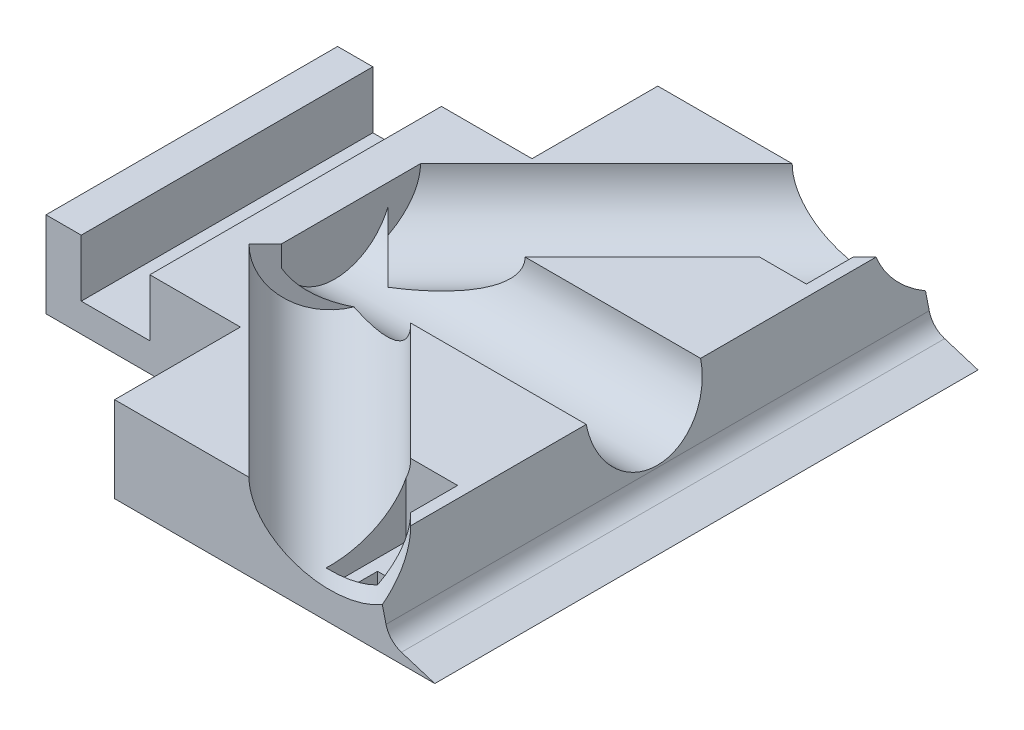
SolidWorks part; units mm, degrees
ref_plane "Front Plane" through (0, 0, 0) normal (0, 0, 1) x (1, 0, 0)
ref_plane "Top Plane" through (0, 0, 0) normal (0, 1, 0) x (1, 0, 0)
ref_plane "Right Plane" through (0, 0, 0) normal (1, 0, 0) x (0, 0, -1)
sketch "Sketch1" plane through (0, 0, 0) normal (0, 1, 0) x (1, 0, 0)
  line L1 (-45, -47.5) -> (45, -47.5)
  line L2 (-45, -47.5) -> (-45, 47.5)
  line L3 (-45, 47.5) -> (45, 47.5)
  line L4 (45, -47.5) -> (45, 47.5)
  line L5 (-45, -47.5) -> (45, 47.5) construction
  line L6 (-45, 47.5) -> (45, -47.5) construction
  point P0 (0, 0)
  dimension "D1" = 95
  dimension "D2" = 90
extrude "Boss-Extrude1" add sketch "Sketch1" along normal blind 20
sketch "Sketch2" plane through (45, 0, 0) normal (1, 0, 0) x (0, 0, -1)
  line L0 (-47.5, 0) -> (47.5, 0) construction
  line L1 (47.5, 20) -> (47.5, 0) construction
  circle A0 centre (0, 13) radius 10
  dimension "D1" = 13
  dimension "D2" = 47.5
extrude "Cut-Extrude2" cut sketch "Sketch2" against normal blind 70
sketch "Sketch3" plane through (0, 0, 47.5) normal (0, 0, 1) x (1, 0, 0)
  line L0 (45, 0) -> (37.4211, 1.8993)
  line L1 (37.4211, 1.8993) -> (30.2523, 20)
  line L2 (-45, 20) -> (45, 20) construction
  line L4 (30.2523, 20) -> (45, 20)
  line L7 (45, 20) -> (45, 0)
extrude "Cut-Extrude3" cut sketch "Sketch3" against normal blind 100
sketch "Sketch5" plane through (0, 0, 47.5) normal (0, 0, 1) x (1, 0, 0)
  line L0 (-45, 0) -> (45, 0) construction
  line L1 (-26.8384, 19) -> (-38.8384, 19)
  line L2 (-26.8384, 19) -> (-26.8384, 3)
  line L3 (-26.8384, 3) -> (-38.8384, 3)
  line L4 (-38.8384, 19) -> (-38.8384, 3)
  dimension "D1" = 12
  dimension "D2" = 3
  dimension "D3" = 16
extrude "Cut-Extrude5" cut sketch "Sketch5" against normal blind 100
fillet "Fillet2" radius 10 1 edges at (37.4211, 1.8993, 0)
sketch "Sketch6" plane through (0, 20, 0) normal (0, 1, 0) x (1, 0, 0)
  line L0 (30.2523, 47.5) -> (-45, 47.5) construction
  line L1 (-45, -47.5) -> (-21, -47.5)
  line L2 (-45, -47.5) -> (-45, 47.5)
  line L3 (-45, 47.5) -> (-21, 47.5)
  line L4 (-21, -47.5) -> (-21, 47.5)
  dimension "D1" = 24
extrude "Boss-Extrude2" add sketch "Sketch6" along normal blind 24
sketch "Sketch7" plane through (0, 20, 0) normal (0, 1, 0) x (1, 0, 0)
  line L0 (-21, -47.5) -> (30.2523, -47.5) construction
  line L1 (-19, -45.5) -> (28.2523, -45.5)
  line L2 (-19, -45.5) -> (-19, -11.5014)
  line L3 (-19, -11.5014) -> (28.2523, -11.5014)
  line L4 (28.2523, -45.5) -> (28.2523, -11.5014)
  line L5 (30.2523, -7.1414) -> (-21, -7.1414) construction
  line L6 (-21, -47.5) -> (-21, -7.1414) construction
  line L7 (30.2523, -7.1414) -> (30.2523, -47.5) construction
  dimension "D1" = 2
  dimension "D2" = 4.36
  dimension "D3" = 2
  dimension "D4" = 2
  dimension "D5" = 33.9986
extrude "Cut-Extrude7" cut sketch "Sketch7" against normal blind 17
sketch "Sketch8" plane through (0, 20, 0) normal (0, 1, 0) x (1, 0, 0)
  line L0 (30.2523, 47.5) -> (-21, 47.5) construction
  line L1 (-19, 11.5) -> (28.2523, 11.5)
  line L2 (-19, 11.5) -> (-19, 45.5)
  line L3 (-19, 45.5) -> (28.2523, 45.5)
  line L4 (28.2523, 11.5) -> (28.2523, 45.5)
  line L5 (30.2523, 47.5) -> (30.2523, 7.1414) construction
  line L6 (-21, 7.1414) -> (-21, 47.5) construction
  dimension "D1" = 2
  dimension "D2" = 34
  dimension "D3" = 2
  dimension "D4" = 2
extrude "Cut-Extrude8" cut sketch "Sketch8" against normal blind 17
sketch "Sketch10" plane through (-21, 0, 0) normal (1, 0, 0) x (0, 0, -1)
  line L1 (-47.5, 44) -> (47.5, 44)
  line L2 (-47.5, 44) -> (-47.5, 20)
  line L3 (-47.5, 20) -> (47.5, 20)
  line L4 (47.5, 44) -> (47.5, 20)
extrude "Boss-Extrude3" add sketch "Sketch10" along normal blind 25
sketch "Sketch12" plane through (-45, 0, 0) normal (-1, 0, 0) x (0, 0, 1)
  line L1 (47.5, 0) -> (25.5, 0)
  line L2 (47.5, 0) -> (47.5, 32)
  line L3 (47.5, 32) -> (25.5, 32)
  line L4 (25.5, 0) -> (25.5, 32)
  dimension "D1" = 32
  dimension "D2" = 22
extrude "Cut-Extrude9" cut sketch "Sketch12" against normal blind 34
sketch "Sketch13" plane through (-45, 0, 0) normal (-1, 0, 0) x (0, 0, 1)
  line L1 (-47.5, 0) -> (-25.5, 0)
  line L2 (-47.5, 0) -> (-47.5, 32)
  line L3 (-47.5, 32) -> (-25.5, 32)
  line L4 (-25.5, 0) -> (-25.5, 32)
  dimension "D1" = 22
  dimension "D2" = 32
extrude "Cut-Extrude10" cut sketch "Sketch13" against normal blind 34
sketch "Sketch14" plane through (0, 0, -47.5) normal (0, 0, -1) x (-1, 0, 0)
  line L0 (11, 32) -> (45, 32) construction
  circle A0 centre (31.5228, 44) radius 10
  dimension "D1" = 12
extrude "Cut-Extrude11" cut sketch "Sketch14" against normal blind 100
sketch "Sketch18" plane through (0, 0, -47.5) normal (0, 0, -1) x (-1, 0, 0)
  line L0 (11, 32) -> (45, 32) construction
  line L1 (-4, 44) -> (15.5228, 44)
  line L2 (-4, 44) -> (-4, 32)
  line L3 (-4, 32) -> (15.5228, 32)
  line L4 (15.5228, 44) -> (15.5228, 32)
  dimension "D1" = 6
extrude "Cut-Extrude13" cut sketch "Sketch18" against normal blind 100
sketch "Sketch19" plane through (-25, 0, 0) normal (1, 0, 0) x (0, 0, -1)
  circle A0 centre (0, 13) radius 10
  arc A1 (-7.1414, 20) -> (7.1414, 20) centre (0, 13) ccw construction
  dimension "D1" = 0
extrude "Boss-Extrude5" add sketch "Sketch19" along normal blind 60
sketch "Sketch20" plane through (0, 0, 47.5) normal (0, 0, 1) x (1, 0, 0)
  line L1 (30.2523, 20) -> (45, 20)
  line L2 (30.2523, 20) -> (30.2523, 0)
  line L3 (30.2523, 0) -> (45, 0)
  line L4 (45, 20) -> (45, 0)
extrude "Boss-Extrude6" add sketch "Sketch20" against normal blind 95
sketch "Sketch21" plane through (0, 20, 0) normal (0, 1, 0) x (1, 0, 0)
  line L1 (45, -47.5) -> (4, -47.5)
  line L2 (45, -47.5) -> (45, 47.5)
  line L3 (45, 47.5) -> (4, 47.5)
  line L4 (4, -47.5) -> (4, 47.5)
extrude "Cut-Extrude16" cut sketch "Sketch21" along normal blind 17
sketch "Sketch23" plane through (0, 0, 47.5) normal (0, 0, 1) x (1, 0, 0)
  line L1 (-11, 32) -> (4, 32)
  line L2 (-11, 32) -> (-11, 20)
  line L3 (-11, 20) -> (4, 20)
  line L4 (4, 32) -> (4, 20)
extrude "Cut-Extrude17" cut sketch "Sketch23" against normal blind 100
sketch "Sketch29" plane through (0, 0, 47.5) normal (0, 0, 1) x (1, 0, 0)
  line L1 (-45, 32) -> (-3.6177, 32)
  line L2 (-45, 32) -> (-45, 73.2631)
  line L3 (-45, 73.2631) -> (-3.6177, 73.2631)
  line L4 (-3.6177, 32) -> (-3.6177, 73.2631)
extrude "Cut-Extrude22" cut sketch "Sketch29" against normal blind 100
sketch "Sketch30" plane through (0, 0, 25.5) normal (0, 0, 1) x (1, 0, 0)
  line L1 (-11, 32) -> (-19, 32)
  line L2 (-11, 32) -> (-11, 20)
  line L3 (-11, 20) -> (-19, 20)
  line L4 (-19, 32) -> (-19, 20)
extrude "Cut-Extrude23" cut sketch "Sketch30" against normal blind 100
sketch "Sketch31" plane through (0, 20, 0) normal (0, 1, 0) x (1, 0, 0)
  line L1 (-19, -11.5014) -> (28.2523, -11.5014)
  line L2 (-19, -11.5014) -> (-19, 11.5)
  line L3 (-19, 11.5) -> (28.2523, 11.5)
  line L4 (28.2523, -11.5014) -> (28.2523, 11.5)
extrude "Cut-Extrude24" cut sketch "Sketch31" against normal blind 17
sketch "Sketch33" plane through (0, 3, 0) normal (0, 1, 0) x (1, 0, 0)
  line L1 (-11, -45.5) -> (28.2523, -45.5)
  line L2 (-11, -45.5) -> (-11, 45.5)
  line L3 (-11, 45.5) -> (28.2523, 45.5)
  line L4 (28.2523, -45.5) -> (28.2523, 45.5)
extrude "Boss-Extrude7" add sketch "Sketch33" along normal blind 17
sketch "Sketch34" plane through (0, 3, 0) normal (0, 1, 0) x (1, 0, 0)
  line L0 (-19, -25.5) -> (-11, -25.5) construction
  line L1 (-11, 25.5) -> (-19, 25.5)
  line L2 (-11, 25.5) -> (-11, -25.5)
  line L3 (-11, -25.5) -> (-19, -25.5)
  line L4 (-19, 25.5) -> (-19, -25.5)
extrude "Boss-Extrude8" add sketch "Sketch34" along normal blind 17
sketch "Sketch35" plane through (0, 20, 0) normal (0, 1, 0) x (1, 0, 0)
  line L0 (45, -64.5) -> (62, -47.5)
  line L1 (45, -47.5) -> (62, -47.5)
  line L2 (45, -47.5) -> (45, -64.5)
  dimension "D1" = 17
  dimension "D2" = 17
extrude "Boss-Extrude10" add sketch "Sketch35" against normal blind 20 separate body
sketch "Sketch36" plane through (0, 20, 0) normal (0, 1, 0) x (1, 0, 0)
  line L0 (62, 47.5) -> (45, 64.5)
  line L1 (45, 47.5) -> (62, 47.5)
  line L2 (45, 47.5) -> (45, 64.5)
  dimension "D1" = 17
  dimension "D2" = 17
extrude "Boss-Extrude13" add sketch "Sketch36" against normal blind 20 separate body contours L0 L2 L1
sketch "Sketch43" plane through (54.75, 0, 54.75) normal (0.7071, 0, 0.7071) x (0.7071, 0, -0.7071)
  line L0 (-13.7886, 0) -> (10.253, 0) construction
  line L1 (10.253, 0) -> (10.253, 20) construction
  circle A0 centre (-14.747, 13) radius 10
  dimension "D1" = 13
  dimension "D2" = 25
extrude "Cut-Extrude35" cut sketch "Sketch43" against normal blind 85
sketch "Sketch44" plane through (54.75, 0, -54.75) normal (0.7071, 0, -0.7071) x (-0.7071, 0, -0.7071)
  line L0 (-10.253, 0) -> (13.7886, 0) construction
  line L1 (-10.253, 0) -> (-10.253, 20) construction
  circle A0 centre (14.747, 13) radius 10
  dimension "D1" = 13
  dimension "D2" = 25
extrude "Cut-Extrude36" cut sketch "Sketch44" against normal blind 85
sketch "Sketch45" plane through (0, 20, 0) normal (0, 1, 0) x (1, 0, 0)
  line L1 (45, -47.5) -> (70.4011, -47.5)
  line L2 (45, -47.5) -> (45, -70.3456)
  line L3 (45, -70.3456) -> (70.4011, -70.3456)
  line L4 (70.4011, -47.5) -> (70.4011, -70.3456)
extrude "Cut-Extrude37" cut sketch "Sketch45" against normal blind 85
sketch "Sketch46" plane through (0, 20, 0) normal (0, 1, 0) x (1, 0, 0)
  line L1 (45, 47.5) -> (66.6361, 47.5)
  line L2 (45, 47.5) -> (45, 69.6416)
  line L3 (45, 69.6416) -> (66.6361, 69.6416)
  line L4 (66.6361, 47.5) -> (66.6361, 69.6416)
extrude "Cut-Extrude38" cut sketch "Sketch46" against normal blind 85
sketch "Sketch48" plane through (45, 0, 0) normal (1, 0, 0) x (0, 0, -1)
  line L0 (-47.5, 0) -> (47.5, 0) construction
  line L1 (47.5, 0) -> (47.5, 20) construction
  circle A0 centre (0, 13) radius 10
  dimension "D1" = 13
  dimension "D2" = 47.5
extrude "Cut-Extrude40" cut sketch "Sketch48" against normal blind 65
sketch "Sketch49" plane through (0, 0, -47.5) normal (0, 0, -1) x (-1, 0, 0)
  circle A0 centre (-68.1577, 31.3858) radius 38.8043
extrude "Cut-Extrude41" cut sketch "Sketch49" against normal blind 100
sketch "Sketch50" plane through (0, 0, 0) normal (0, -1, 0) x (-1, 0, 0)
  line L0 (11, -47.5) -> (-45, -47.5) construction
  line L1 (-38, -45.5) -> (-28, -45.5)
  line L2 (-38, -45.5) -> (-38, -28.5)
  line L3 (-38, -28.5) -> (-28, -28.5)
  line L4 (-28, -45.5) -> (-28, -28.5)
  line L5 (-45, -47.5) -> (-45, 47.5) construction
  dimension "D1" = 17
  dimension "D2" = 10
  dimension "D3" = 2
  dimension "D4" = 7
extrude "Cut-Extrude43" cut sketch "Sketch50" against normal blind 4
sketch "Sketch51" plane through (0, 0, 0) normal (0, -1, 0) x (-1, 0, 0)
  line L0 (-45, -47.5) -> (-45, 47.5) construction
  line L1 (-38, 28.5) -> (-28, 28.5)
  line L2 (-38, 28.5) -> (-38, 45.5)
  line L3 (-38, 45.5) -> (-28, 45.5)
  line L4 (-28, 28.5) -> (-28, 45.5)
  line L5 (-45, 47.5) -> (11, 47.5) construction
  dimension "D1" = 17
  dimension "D2" = 10
  dimension "D3" = 7
  dimension "D4" = 2
extrude "Cut-Extrude44" cut sketch "Sketch51" against normal blind 4
sketch "Sketch52" plane through (0, 20, 0) normal (0, 1, 0) x (1, 0, 0)
  line L0 (31.0614, -7.1414) -> (-3.6144, -7.1414) construction
  line L1 (31.0614, -41.8172) -> (31.0614, -7.1414) construction
  circle A0 centre (26.0614, -27.1414) radius 3
  dimension "D1" = 20
  dimension "D2" = 5
extrude "Cut-Extrude45" cut sketch "Sketch52" against normal blind 100
sketch "Sketch53" plane through (0, 20, 0) normal (0, 1, 0) x (1, 0, 0)
  line L0 (-3.6144, 7.1414) -> (31.0614, 7.1414) construction
  line L1 (31.0614, 7.1414) -> (31.0614, 41.8172) construction
  circle A0 centre (26.0614, 27.1414) radius 3
  dimension "D1" = 20
  dimension "D2" = 5
extrude "Cut-Extrude46" cut sketch "Sketch53" against normal blind 100
sketch "Sketch54" plane through (-20, 0, 0) normal (1, 0, 0) x (0, 0, -1)
  line L1 (-10, 13) -> (66.5355, 13)
  line L3 (-10, 31.15) -> (66.5355, 31.15)
  line L4 (66.5355, 13) -> (66.5355, 31.15)
  line L5 (-10, 13) -> (-56.0211, 13)
  line L7 (-10, 31.15) -> (-56.0211, 31.15)
  line L8 (-56.0211, 13) -> (-56.0211, 31.15)
  arc A0 (-7.1414, 20) -> (7.1414, 20) centre (0, 13) ccw construction
extrude "Cut-Extrude47" cut sketch "Sketch54" along normal blind 300
sketch "Sketch55" plane through (0, 0, 25.5) normal (0, 0, 1) x (1, 0, 0)
  line L1 (-38.8384, 19) -> (-69.436, 19)
  line L3 (-38.8384, 41.9777) -> (-69.436, 41.9777)
  line L4 (-69.436, 19) -> (-69.436, 41.9777)
  line L5 (-38.8384, 19) -> (-7.7562, 19)
  line L6 (-38.8384, 41.9777) -> (-38.8384, 52.6636)
  line L7 (-38.8384, 52.6636) -> (-7.7562, 52.6636)
  line L8 (-7.7562, 19) -> (-7.7562, 52.6636)
extrude "Cut-Extrude48" cut sketch "Sketch55" against normal blind 300
sketch "Sketch57" plane through (0, 4, 0) normal (0, -1, 0) x (-1, 0, 0)
  line L1 (-38, -45.5) -> (-28, -45.5)
  line L2 (-38, -45.5) -> (-38, -28.5)
  line L3 (-38, -28.5) -> (-28, -28.5)
  line L4 (-28, -45.5) -> (-28, -28.5)
  line L5 (-38, 28.5) -> (-28, 28.5)
  line L6 (-38, 28.5) -> (-38, 45.5)
  line L7 (-38, 45.5) -> (-28, 45.5)
  line L8 (-28, 28.5) -> (-28, 45.5)
  dimension "D1" = 10
  dimension "D2" = 17
  dimension "D3" = 17
extrude "Boss-Extrude15" add sketch "Sketch57" along normal blind 4
sketch "Sketch58" plane through (0, 0, 0) normal (0, -1, 0) x (-1, 0, 0)
  line L0 (11, 25.5) -> (11, 47.5)
  line L1 (45, 25.5) -> (11, 25.5)
  line L2 (45, 25.5) -> (45, -25.5)
  line L3 (45, -25.5) -> (11, -25.5)
  line L5 (11, -47.5) -> (-45, -47.5)
  line L6 (11, -47.5) -> (11, -25.5)
  line L7 (11, 47.5) -> (-45, 47.5)
  line L8 (-45, -47.5) -> (-45, 47.5)
extrude "Boss-Extrude16" add sketch "Sketch58" along normal blind 4
sketch "Sketch60" plane through (0, -4, 0) normal (0, -1, 0) x (-1, 0, 0)
  line L0 (11, -25.5) -> (11, -47.5)
  line L1 (-45, 47.5) -> (11, 47.5)
  line L2 (-45, 47.5) -> (-45, -47.5)
  line L3 (-45, -47.5) -> (11, -47.5)
  line L4 (11, 47.5) -> (11, 25.5)
  line L5 (45, -25.5) -> (11, -25.5)
  line L6 (45, -25.5) -> (45, 25.5)
  line L7 (45, 25.5) -> (11, 25.5)
extrude "Cut-Extrude49" cut sketch "Sketch60" against normal blind 2
sketch "Sketch61" plane through (0, 0, -47.5) normal (0, 0, -1) x (-1, 0, 0)
  line L0 (-45, -2) -> (-37, 0.5)
  line L1 (-37, 0.5) -> (-33.9855, 13)
  line L2 (-33.9855, 13) -> (-46.9602, 4.2727)
  line L3 (-46.9602, 4.2727) -> (-45, -2)
  line L4 (11, -2) -> (-45, -2) construction
  dimension "D1" = 2.5
  dimension "D2" = 8
extrude "Cut-Extrude51" cut sketch "Sketch61" against normal blind 100
fillet "Fillet3" radius 4 1 edges at (37, 0.5, 0)
sketch "Sketch63" plane through (-5.3541, 0, 5.3541) normal (0.7071, 0, -0.7071) x (-0.7071, 0, -0.7071)
  circle A0 centre (14.747, 13) radius 10
extrude "Cut-Extrude52" cut sketch "Sketch63" along normal blind 65
sketch "Sketch65" plane through (-5.3541, 0, -5.3541) normal (0.7071, 0, 0.7071) x (0.7071, 0, -0.7071)
  circle A0 centre (-14.747, 13) radius 10
extrude "Cut-Extrude53" cut sketch "Sketch65" along normal blind 65
sketch "Sketch66" plane through (0, 0, -25.5) normal (0, 0, -1) x (-1, 0, 0)
  line L1 (20, 13) -> (45, 13)
  line L2 (20, 13) -> (20, 19)
  line L3 (20, 19) -> (45, 19)
  line L4 (45, 13) -> (45, 19)
extrude "Cut-Extrude54" cut sketch "Sketch66" against normal blind 65
sketch "Sketch68" plane through (0, 13, 0) normal (0, 1, 0) x (1, 0, 0)
  line L1 (-26.8384, 25.5) -> (-20, 25.5)
  line L2 (-26.8384, 25.5) -> (-26.8384, -9.2918)
  line L4 (-20, 25.5) -> (-20, -9.2918)
  line L6 (-20, -9.2918) -> (-20, -25.5)
  line L7 (-20, -25.5) -> (-26.8384, -25.5)
  line L8 (-26.8384, -9.2918) -> (-26.8384, -25.5)
extrude "Boss-Extrude17" add sketch "Sketch68" against normal blind 15
sketch "Sketch70" plane through (0, 13, 0) normal (0, 1, 0) x (1, 0, 0)
  circle A0 centre (26.0614, 27.1414) radius 3
extrude "Boss-Extrude18" add sketch "Sketch70" against normal blind 15
sketch "Sketch72" plane through (0, 13, 0) normal (0, 1, 0) x (1, 0, 0)
  line L0 (33.9855, 10) -> (33.9855, 40.6987) construction
  line L1 (22.9855, 44.5) -> (31.9855, 44.5)
  line L2 (22.9855, 44.5) -> (22.9855, 30.5)
  line L3 (22.9855, 30.5) -> (31.9855, 30.5)
  line L4 (31.9855, 44.5) -> (31.9855, 30.5)
  dimension "D1" = 2
  dimension "D2" = 3
  dimension "D3" = 14
  dimension "D4" = 9
extrude "Cut-Extrude56" cut sketch "Sketch72" against normal blind 12
sketch "Sketch73" plane through (0, 0, 0) normal (0, 1, 0) x (1, 0, 0)
  circle A0 centre (26.0614, -27.1414) radius 3
extrude "Boss-Extrude20" add sketch "Sketch73" along normal blind 13
sketch "Sketch74" plane through (0, 13, 0) normal (0, 1, 0) x (1, 0, 0)
  line L1 (22.9855, -30.5) -> (31.9855, -30.5)
  line L2 (22.9855, -30.5) -> (22.9855, -44.5)
  line L3 (22.9855, -44.5) -> (31.9855, -44.5)
  line L4 (31.9855, -30.5) -> (31.9855, -44.5)
  dimension "D1" = 14
  dimension "D2" = 9
  dimension "D3" = 2
  dimension "D4" = 3
extrude "Cut-Extrude57" cut sketch "Sketch74" against normal blind 13
sketch "Sketch75" plane through (0, 0, 0) normal (0, 1, 0) x (1, 0, 0)
  line L0 (22.9855, -30.5) -> (22.9855, -44.5) construction
  line L1 (24.9855, -42.5) -> (29.9855, -42.5)
  line L2 (24.9855, -42.5) -> (24.9855, -37.5)
  line L3 (24.9855, -37.5) -> (29.9855, -37.5)
  line L4 (29.9855, -42.5) -> (29.9855, -37.5)
  line L5 (31.9855, -44.5) -> (31.9855, -30.5) construction
  line L6 (22.9855, -44.5) -> (31.9855, -44.5) construction
  line L7 (22.9855, 44.5) -> (31.9855, 44.5) construction
  line L8 (29.9855, 37.5) -> (24.9855, 37.5)
  line L9 (29.9855, 37.5) -> (29.9855, 42.5)
  line L10 (29.9855, 42.5) -> (24.9855, 42.5)
  line L11 (24.9855, 37.5) -> (24.9855, 42.5)
  dimension "D1" = 2
  dimension "D2" = 2
  dimension "D3" = 2
  dimension "D4" = 5
  dimension "D5" = 5
  dimension "D6" = 2
extrude "Cut-Extrude58" cut sketch "Sketch75" against normal blind 13
sketch "Sketch76" plane through (0, 0, 0) normal (0, -1, 0) x (-1, 0, 0)
  line L0 (-24.9855, 42.5) -> (-24.9855, 37.5) construction
  line L1 (-29.9855, 37.5) -> (-24.9855, 37.5)
  line L2 (-29.9855, 37.5) -> (-29.9855, 42.5)
  line L3 (-29.9855, 42.5) -> (-24.9855, 42.5)
  line L4 (-24.9855, 37.5) -> (-24.9855, 42.5)
extrude "Cut-Extrude59" cut sketch "Sketch76" against normal blind 13
sketch "Sketch77" plane through (0, 13, 0) normal (0, 1, 0) x (1, 0, 0)
  line L0 (22.9855, -39.5) -> (-20, 0)
  line L1 (22.9855, -30.5) -> (22.9855, -44.5) construction
  line L2 (-20, -9.2918) -> (-20, 9.2918) construction
  line L3 (22.9855, -39.5) -> (22.9855, -44.5)
  line L4 (22.9855, -44.5) -> (-20, -5)
  line L5 (-20, -14.9975) -> (-20, 14.9975) construction
  line L6 (-20, -5) -> (-20, 0)
  dimension "D2" = 5
  dimension "D3" = 5
extrude "Cut-Extrude63" cut sketch "Sketch77" against normal blind 13
sketch "Sketch84" plane through (0, 1, 0) normal (0, 1, 0) x (1, 0, 0)
  line L1 (22.9855, 44.5) -> (31.9855, 44.5)
  line L2 (22.9855, 44.5) -> (22.9855, 30.5)
  line L3 (22.9855, 30.5) -> (31.9855, 30.5)
  line L4 (31.9855, 44.5) -> (31.9855, 30.5)
  line L5 (29.9855, 37.5) -> (24.9855, 37.5)
  line L6 (29.9855, 37.5) -> (29.9855, 42.5)
  line L7 (29.9855, 42.5) -> (24.9855, 42.5)
  line L8 (24.9855, 37.5) -> (24.9855, 42.5)
extrude "Cut-Extrude71" cut sketch "Sketch84" against normal blind 1
sketch "Sketch86" plane through (0, 0, 0) normal (0, 1, 0) x (1, 0, 0)
  line L0 (-20, 0) -> (22.9855, -39.5)
  line L1 (-20, -14.9975) -> (-20, 14.9975) construction
  line L2 (22.9855, -39.5) -> (22.9855, -44.5)
  line L3 (22.9855, -44.5) -> (-20, -5)
  line L4 (-20, -5) -> (-20, 0)
extrude "Boss-Extrude21" add sketch "Sketch86" along normal blind 10
sketch "Sketch87" plane through (-5.3541, 0, -5.3541) normal (0.7071, 0, 0.7071) x (0.7071, 0, -0.7071)
  circle A0 centre (-14.747, 13) radius 10
extrude "Cut-Extrude73" cut sketch "Sketch87" along normal blind 100
sketch "Sketch88" plane through (-20, 0, 0) normal (1, 0, 0) x (0, 0, -1)
  circle A0 centre (0, 13) radius 10
extrude "Cut-Extrude74" cut sketch "Sketch88" along normal blind 100
